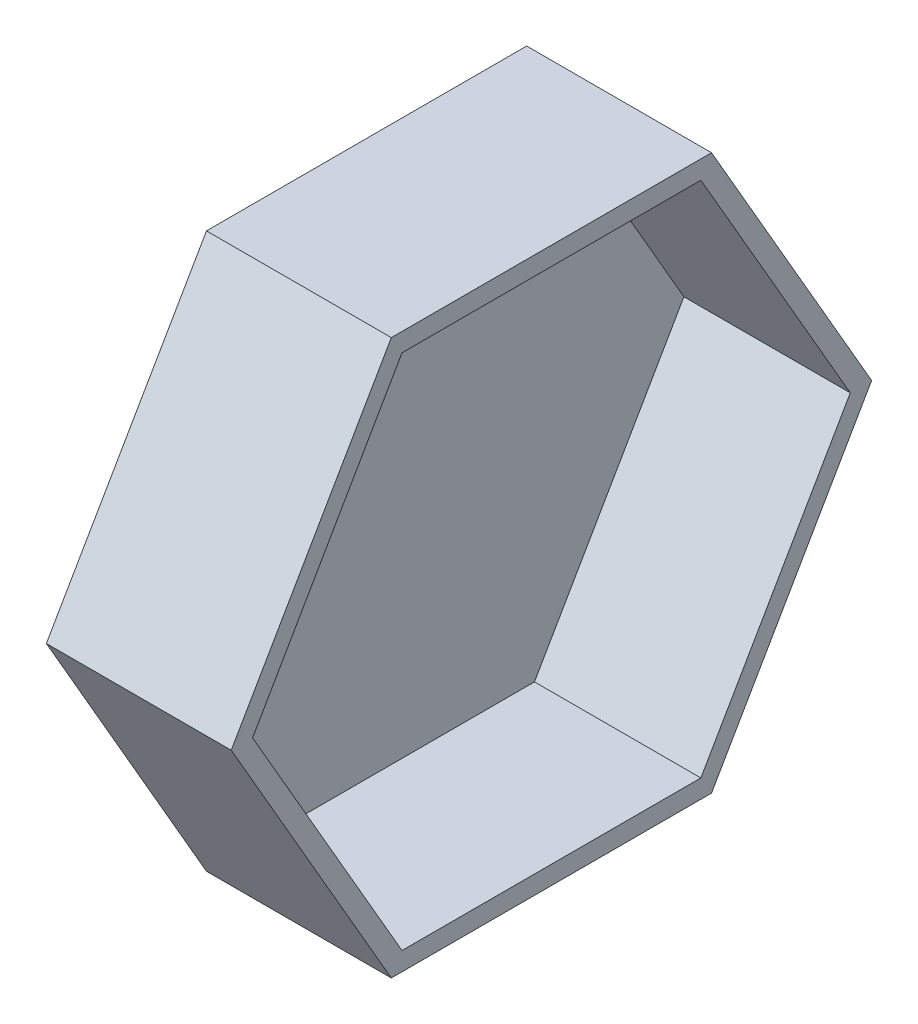
SolidWorks part; units mm, degrees
ref_plane "Plano frontal" through (0, 0, 0) normal (0, 0, 1) x (1, 0, 0)
ref_plane "Plano superior" through (0, 0, 0) normal (0, 1, 0) x (1, 0, 0)
ref_plane "Plano direito" through (0, 0, 0) normal (1, 0, 0) x (0, 0, -1)
sketch "Esboço1" plane through (0, 0, 0) normal (1, 0, 0) x (0, 0, -1)
  line L1 (173.2051, 0) -> (86.6025, 150)
  line L2 (86.6025, 150) -> (-86.6025, 150)
  line L3 (-86.6025, 150) -> (-173.2051, 0)
  line L4 (-173.2051, 0) -> (-86.6025, -150)
  line L5 (-86.6025, -150) -> (86.6025, -150)
  line L6 (86.6025, -150) -> (173.2051, 0)
  circle A0 centre (0, 0) radius 150 construction
  dimension "D1" = 300
extrude "Ressalto-extrusão1" add sketch "Esboço1" along normal mid plane 100
shell "Casca1" thickness 10
